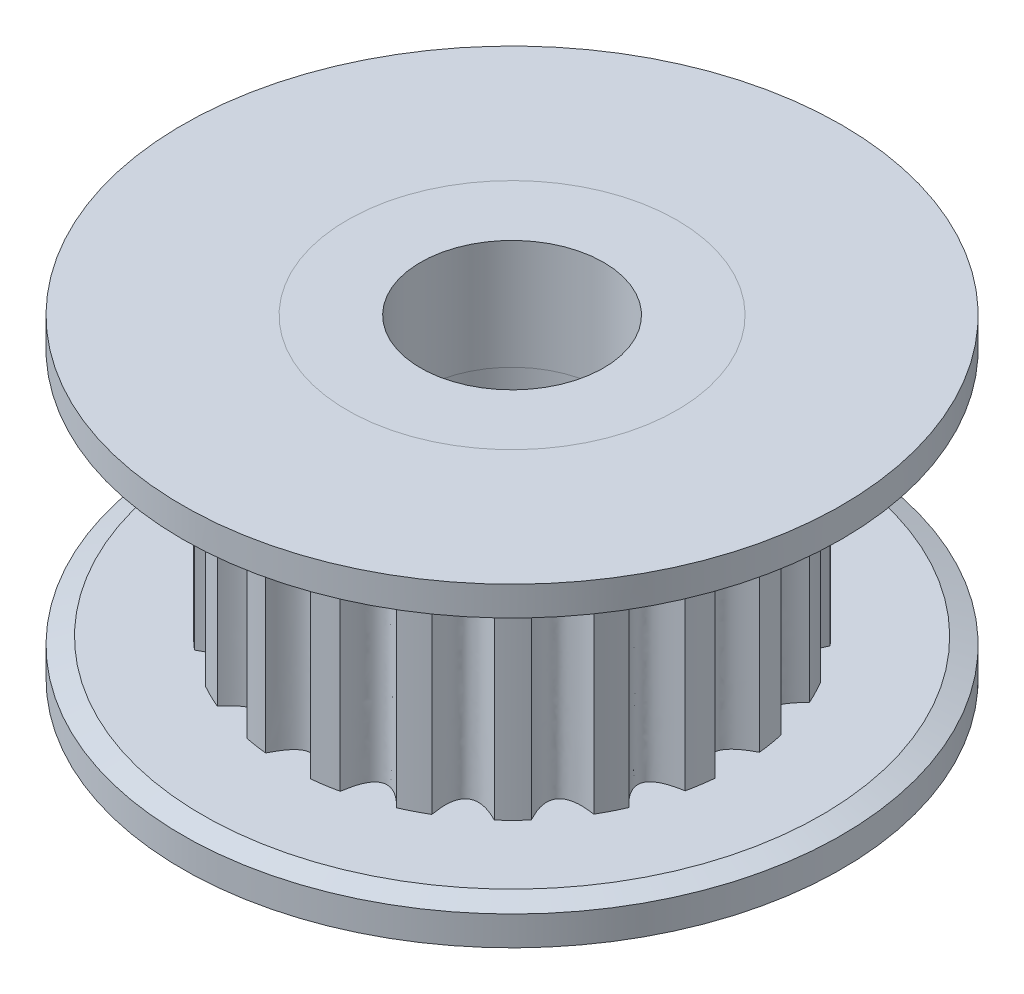
SolidWorks part; units mm, degrees
ref_plane "Plano frontal" through (0, 0, 0) normal (0, 0, 1) x (1, 0, 0)
ref_plane "Plano superior" through (0, 0, 0) normal (0, 1, 0) x (1, 0, 0)
ref_plane "Plano direito" through (0, 0, 0) normal (1, 0, 0) x (0, 0, -1)
sketch "Esboço1" plane through (0, 0, 0) normal (0, 0, 1) x (1, 0, 0)
  line L0 (-4.5, 0) -> (-9, 0)
  line L1 (-9, 0) -> (-9, 1)
  line L2 (-9, 1) -> (-6.15, 1)
  line L3 (-6.15, 1) -> (-6.15, 7.6)
  line L4 (-6.15, 7.6) -> (-9, 7.6)
  line L5 (-9, 7.6) -> (-9, 8.6)
  line L6 (-9, 8.6) -> (-4.5, 8.6)
  line L7 (-4.5, 0) -> (-4.5, 3)
  line L8 (-4.5, 3) -> (-2.5, 3)
  line L9 (-2.5, 3) -> (-2.5, 5.6)
  line L10 (-2.5, 5.6) -> (-4.5, 5.6)
  line L11 (-4.5, 5.6) -> (-4.5, 8.6)
  line L12 (0, 0) -> (0, 8.6) construction
  dimension "D1" = 1
  dimension "D2" = 9
  dimension "D3" = 6.6
  dimension "D4" = 6.15
  dimension "D5" = 4.5
  dimension "D6" = 2.5
  dimension "D7" = 3
revolve "Revolução1" add sketch "Esboço1" angle 360 about L12
chamfer "Chanfro1" distance 0.2 angle 70 1 edges at (0, 1, -9)
chamfer "Chanfro2" distance 0.2 angle 70 1 edges at (0, 7.6, -9)
sketch "Esboço2" plane through (0, 0, 0) normal (0, 0, 1) x (1, 0, 0)
  line L0 (-2.5, 0) -> (-2.5, 3)
  line L1 (-9, 0) -> (9, 0) construction
  line L2 (-2.5, 3) -> (-4.5, 3)
  line L3 (-4.5, 3) -> (-4.5, 0)
  line L4 (-4.5, 0) -> (-2.5, 0)
  line L5 (9, 8.6) -> (-9, 8.6) construction
  line L6 (-4.5, 5.6) -> (-2.5, 5.6)
  line L7 (-4.5, 5.6) -> (-4.5, 8.6)
  line L8 (-4.5, 8.6) -> (-2.5, 8.6)
  line L9 (-2.5, 5.6) -> (-2.5, 8.6)
  line L10 (0, 0) -> (0, 8.6) construction
  dimension "D1" = 2.5
  dimension "D2" = 4.5
  dimension "D3" = 3
revolve "Revolução2" add sketch "Esboço2" angle 360 about L10
sketch "Esboço3" plane through (0, 7.6, 0) normal (0, -1, 0) x (1, 0, 0)
  line L0 (0, 6.15) -> (0, 5.5) construction
  circle A0 centre (0, 0) radius 6.15 construction
  arc A1 (0.6113, 6.1195) -> (-0.6113, 6.1195) centre (0, 0) ccw
  arc A2 (2.4776, 5.6289) -> (1.3152, 6.0077) centre (0, 0) ccw
  arc A3 (4.0999, 4.584) -> (3.1122, 5.3044) centre (0, 0) ccw
  arc A4 (5.3186, 3.0878) -> (4.6028, 4.0788) centre (0, 0) ccw
  arc A5 (6.0137, 1.2876) -> (5.6402, 2.4517) centre (0, 0) ccw
  arc A6 (6.1167, -0.6394) -> (6.1223, 0.5832) centre (0, 0) ccw
  arc A7 (5.6174, -2.5034) -> (6.0016, -1.3428) centre (0, 0) ccw
  arc A8 (4.5651, -4.1209) -> (5.2901, -3.1365) centre (0, 0) ccw
  arc A9 (3.0634, -5.3328) -> (4.0577, -4.6215) centre (0, 0) ccw
  arc A10 (1.26, -6.0195) -> (2.4258, -5.6514) centre (0, 0) ccw
  arc A11 (-0.6674, -6.1137) -> (0.5551, -6.1249) centre (0, 0) ccw
  arc A12 (-2.5291, -5.6059) -> (-1.3703, -5.9954) centre (0, 0) ccw
  arc A13 (-4.1418, -4.5462) -> (-3.1608, -5.2756) centre (0, 0) ccw
  arc A14 (-5.3468, -3.0389) -> (-4.64, -4.0364) centre (0, 0) ccw
  arc A15 (-6.0253, -1.2324) -> (-5.6625, -2.3998) centre (0, 0) ccw
  arc A16 (-6.1105, 0.6955) -> (-6.1274, -0.5269) centre (0, 0) ccw
  arc A17 (-5.5942, 2.5548) -> (-5.989, 1.3978) centre (0, 0) ccw
  arc A18 (-4.5271, 4.1627) -> (-5.261, 3.185) centre (0, 0) ccw
  arc A19 (-3.0143, 5.3607) -> (-4.0151, 4.6585) centre (0, 0) ccw
  arc A20 (-1.2047, 6.0309) -> (-2.3738, 5.6734) centre (0, 0) ccw
  spline S0 degree 2 poles (0.6113, 6.1195) (0, 4.8805) (-0.6113, 6.1195) knots 0 0 0 1 1 1
  spline S1 degree 2 poles (2.4776, 5.6289) (1.5075, 4.6418) (1.3152, 6.0077) knots 0 0 0 1 1 1
  spline S2 degree 2 poles (4.0999, 4.584) (2.8676, 3.949) (3.1122, 5.3044) knots 0 0 0 1 1 1
  spline S3 degree 2 poles (5.3186, 3.0878) (3.9471, 2.8701) (4.6028, 4.0788) knots 0 0 0 1 1 1
  spline S4 degree 2 poles (6.0137, 1.2876) (4.6405, 1.5105) (5.6402, 2.4517) knots 0 0 0 1 1 1
  spline S5 degree 2 poles (6.1167, -0.6394) (4.8799, 0.0032) (6.1223, 0.5832) knots 0 0 0 1 1 1
  spline S6 degree 2 poles (5.6174, -2.5034) (4.642, -1.5042) (6.0016, -1.3428) knots 0 0 0 1 1 1
  spline S7 degree 2 poles (4.5651, -4.1209) (3.9501, -2.8643) (5.2901, -3.1365) knots 0 0 0 1 1 1
  spline S8 degree 2 poles (3.0634, -5.3328) (2.872, -3.9441) (4.0577, -4.6215) knots 0 0 0 1 1 1
  spline S9 degree 2 poles (1.26, -6.0195) (1.5132, -4.638) (2.4258, -5.6514) knots 0 0 0 1 1 1
  spline S10 degree 2 poles (-0.6674, -6.1137) (0.0066, -4.8782) (0.5551, -6.1249) knots 0 0 0 1 1 1
  spline S11 degree 2 poles (-2.5291, -5.6059) (-1.5004, -4.6412) (-1.3703, -5.9954) knots 0 0 0 1 1 1
  spline S12 degree 2 poles (-4.1418, -4.5462) (-2.8603, -3.9505) (-3.1608, -5.2756) knots 0 0 0 1 1 1
  spline S13 degree 2 poles (-5.3468, -3.0389) (-3.9402, -2.8735) (-4.64, -4.0364) knots 0 0 0 1 1 1
  spline S14 degree 2 poles (-6.0253, -1.2324) (-4.6345, -1.5158) (-5.6625, -2.3998) knots 0 0 0 1 1 1
  spline S15 degree 2 poles (-6.1105, 0.6955) (-4.8754, -0.0103) (-6.1274, -0.5269) knots 0 0 0 1 1 1
  spline S16 degree 2 poles (-5.5942, 2.5548) (-4.6395, 1.4959) (-5.989, 1.3978) knots 0 0 0 1 1 1
  spline S17 degree 2 poles (-4.5271, 4.1627) (-3.9501, 2.8553) (-5.261, 3.185) knots 0 0 0 1 1 1
  spline S18 degree 2 poles (-3.0143, 5.3607) (-2.8747, 3.9351) (-4.0151, 4.6585) knots 0 0 0 1 1 1
  spline S19 degree 2 poles (-1.2047, 6.0309) (-1.5185, 4.6297) (-2.3738, 5.6734) knots 0 0 0 1 1 1
  point P67 (0, 0)
  dimension "D1" = 0.65
  dimension "D3" = 0.6
  dimension "D2" = 20
extrude "Corte-extrusão1" cut sketch "Esboço3" along normal up to surface (6.6 mm away) up to face at (0, 1, -8.4505)
ref_point "Ponto1"
ref_plane "Plano2" through (0, 4.3, 0) normal (0, 1, 0) x (1, 0, 0)
